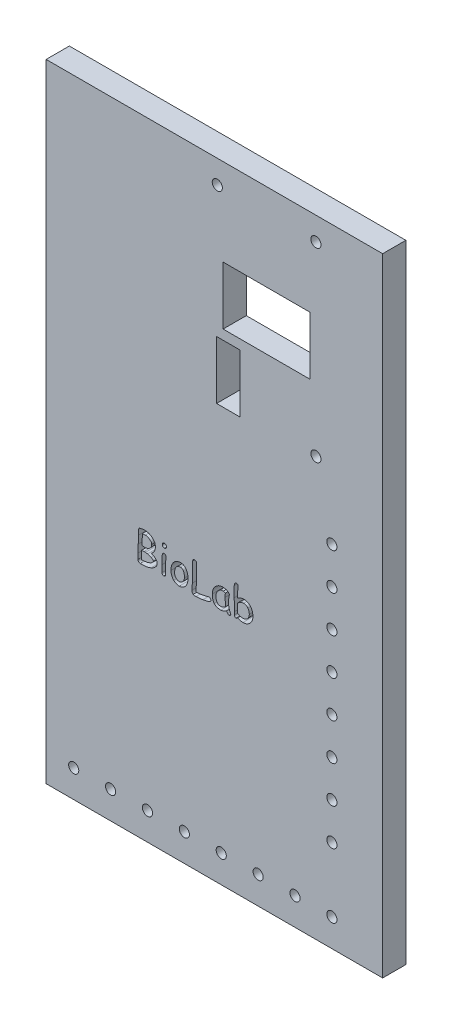
SolidWorks part; units mm, degrees
ref_plane "Plano frontal" through (0, 0, 0) normal (0, 0, 1) x (1, 0, 0)
ref_plane "Plano superior" through (0, 0, 0) normal (0, 1, 0) x (1, 0, 0)
ref_plane "Plano direito" through (0, 0, 0) normal (1, 0, 0) x (0, 0, -1)
sketch "Esboço1" plane through (0, 0, 0) normal (0, 0, 1) x (1, 0, 0)
  line L1 (-58, 108.115) -> (58, 108.115)
  line L2 (-58, 108.115) -> (-58, -108.115)
  line L3 (-58, -108.115) -> (58, -108.115)
  line L4 (58, 108.115) -> (58, -108.115)
  line L5 (-58, 108.115) -> (58, -108.115) construction
  line L6 (-58, -108.115) -> (58, 108.115) construction
  line L7 (0.75, 54.775) -> (8.75, 54.775)
  line L8 (0.75, 54.775) -> (0.75, 34.775)
  line L9 (0.75, 34.775) -> (8.75, 34.775)
  line L10 (8.75, 54.775) -> (8.75, 34.775)
  line L11 (0.75, 54.775) -> (8.75, 34.775) construction
  line L12 (0.75, 34.775) -> (8.75, 54.775) construction
  line L13 (3, 78.115) -> (33, 78.115)
  line L14 (3, 78.115) -> (3, 58.115)
  line L15 (3, 58.115) -> (33, 58.115)
  line L16 (33, 78.115) -> (33, 58.115)
  line L17 (3, 78.115) -> (33, 58.115) construction
  line L18 (3, 58.115) -> (33, 78.115) construction
  circle A0 centre (35, 100.115) radius 1.75
  circle A1 centre (35, 36.115) radius 1.75
  circle A2 centre (1, 100.115) radius 1.75
  point P0 (0, 0)
  point P6 (4.75, 44.775)
  point P11 (4.75, 34.775)
  point P18 (18, 68.115)
  dimension "D7" = 3.5
  dimension "D8" = 3.5
  dimension "D9" = 3.5
  dimension "D10" = 23
  dimension "D11" = 8
  dimension "D12" = 8
  dimension "D13" = 23
  dimension "D14" = 34
  dimension "D15" = 64
  dimension "D16" = 20
  dimension "D18" = 32
  dimension "D1" = 216.23
  dimension "D2" = 116
  dimension "D3" = 8
  dimension "D4" = 20
  dimension "D5" = 53.25
  dimension "D6" = 63.34
  dimension "D17" = 30
  dimension "D19" = 40
extrude "Ressalto-extrusão1" add sketch "Esboço1" along normal blind 8
sketch "Esboço2" plane through (0, 0, 8) normal (0, 0, 1) x (1, 0, 0)
  line L0 (-58, -108.115) -> (58, -108.115) construction
  line L1 (-58, 108.115) -> (-58, -108.115) construction
  circle A0 centre (-48.5, -98.615) radius 1.75
  dimension "D1" = 3.5
  dimension "D2" = 9.5
  dimension "D3" = 9.5
extrude "Corte-extrusão1" cut sketch "Esboço2" against normal blind 100
pattern_linear "Padrão linear1" count 8 spacing 12.7143 along (1, 0, 0) of "Corte-extrusão1"
sketch "Esboço3" plane through (0, 0, 8) normal (0, 0, 1) x (1, 0, 0)
  line L0 (58, -108.115) -> (58, 108.115) construction
  line L1 (58, 108.115) -> (-58, 108.115) construction
  circle A0 centre (40.5, 12.615) radius 1.75
  dimension "D1" = 3.5
  dimension "D2" = 17.5
  dimension "D3" = 95.5
extrude "Corte-extrusão2" cut sketch "Esboço3" against normal blind 100
pattern_linear "Padrão linear2" count 8 spacing 12.7143 along (0, -1, 0) of "Corte-extrusão2"
sketch "Esboço4" plane through (0, 0, 8) normal (0, 0, 1) x (1, 0, 0)
  text T0 "BioLab" font "Comic Sans MS" height 10
extrude "Corte-extrusão3" cut sketch "Esboço4" against normal blind 10
